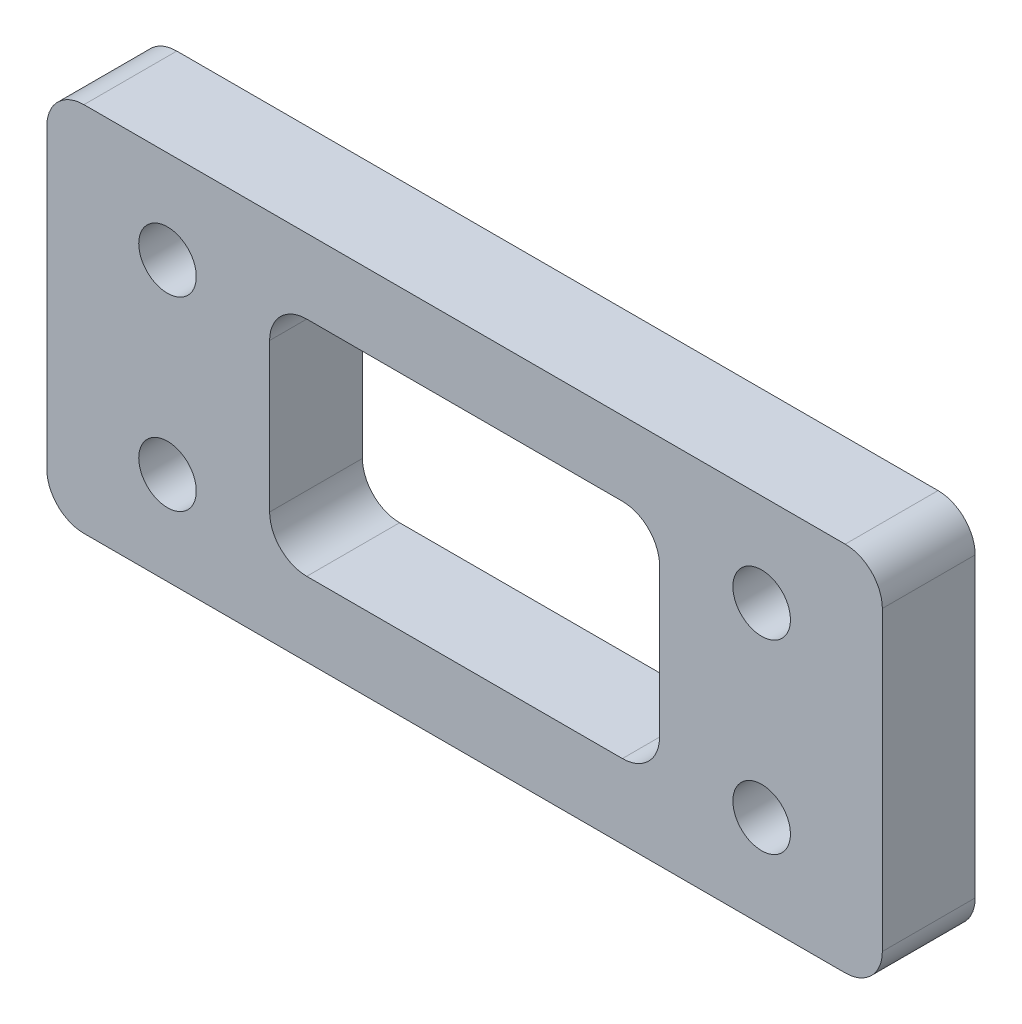
SolidWorks part; units mm, degrees
material "环氧玻璃布层压板"
ref_plane "前视基准面" through (0, 0, 0) normal (0, 0, 1) x (1, 0, 0)
ref_plane "上视基准面" through (0, 0, 0) normal (0, 1, 0) x (1, 0, 0)
ref_plane "右视基准面" through (0, 0, 0) normal (1, 0, 0) x (0, 0, -1)
sketch "草图1" plane through (0, 0, 0) normal (0, 0, 1) x (1, 0, 0)
  line L1 (-22.5, -10) -> (22.5, -10)
  line L2 (-22.5, -10) -> (-22.5, 10)
  line L3 (-22.5, 10) -> (22.5, 10)
  line L4 (22.5, -10) -> (22.5, 10)
  line L5 (0, 10) -> (0, -10) construction
  line L6 (-22.5, 0) -> (22.5, 0) construction
  point P0 (0, 0)
  dimension "D1" = 45
  dimension "D2" = 20
extrude "凸台-拉伸1" add sketch "草图1" along normal mid plane 5
sketch "草图3" plane through (0, 0, 2.5) normal (0, 0, 1) x (1, 0, 0)
  arc A0 (17.6, -5) -> (14.4, -5) centre (16, -5) ccw construction
  arc A1 (17.6, 5) -> (14.4, 5) centre (16, 5) ccw construction
  arc A2 (-14.4, -5) -> (-17.6, -5) centre (-16, -5) ccw construction
  arc A3 (-14.4, 5) -> (-17.6, 5) centre (-16, 5) ccw construction
  arc A4 (17.6, -5) -> (14.4, -5) centre (16, -5) ccw construction
  arc A5 (17.6, 5) -> (14.4, 5) centre (16, 5) ccw construction
  arc A6 (-14.4, -5) -> (-17.6, -5) centre (-16, -5) ccw construction
  arc A7 (-14.4, 5) -> (-17.6, 5) centre (-16, 5) ccw construction
  circle A8 centre (16, 5) radius 1.55
  circle A9 centre (-16, 5) radius 1.55
  circle A10 centre (-16, -5) radius 1.55
  circle A11 centre (16, -5) radius 1.55
  dimension "D1" = 3.1
extrude "切除-拉伸1" cut sketch "草图3" against normal mid plane 65
fillet "圆角1" radius 2 4 edges at (-22.5, -10, 0) (-22.5, 10, 0) (22.5, -10, 0) (22.5, 10, 0)
sketch "草图4" plane through (0, 0, 2.5) normal (0, 0, 1) x (1, 0, 0)
  line L0 (22.5, -8) -> (22.5, 8) construction
  line L1 (-10.5, -6) -> (10.5, -6)
  line L2 (-10.5, -6) -> (-10.5, 6)
  line L3 (-10.5, 6) -> (10.5, 6)
  line L4 (10.5, -6) -> (10.5, 6)
  line L5 (0, 6) -> (0, -6) construction
  line L6 (-10.5, 0) -> (10.5, 0) construction
  line L7 (20.5, 10) -> (-20.5, 10) construction
  point P0 (0, 0)
  dimension "D1" = 12
  dimension "D2" = 4
extrude "切除-拉伸2" cut sketch "草图4" against normal blind 30
fillet "圆角2" radius 2 4 edges at (10.5, -6, 0) (10.5, 6, 0) (-10.5, -6, 0) (-10.5, 6, 0)
